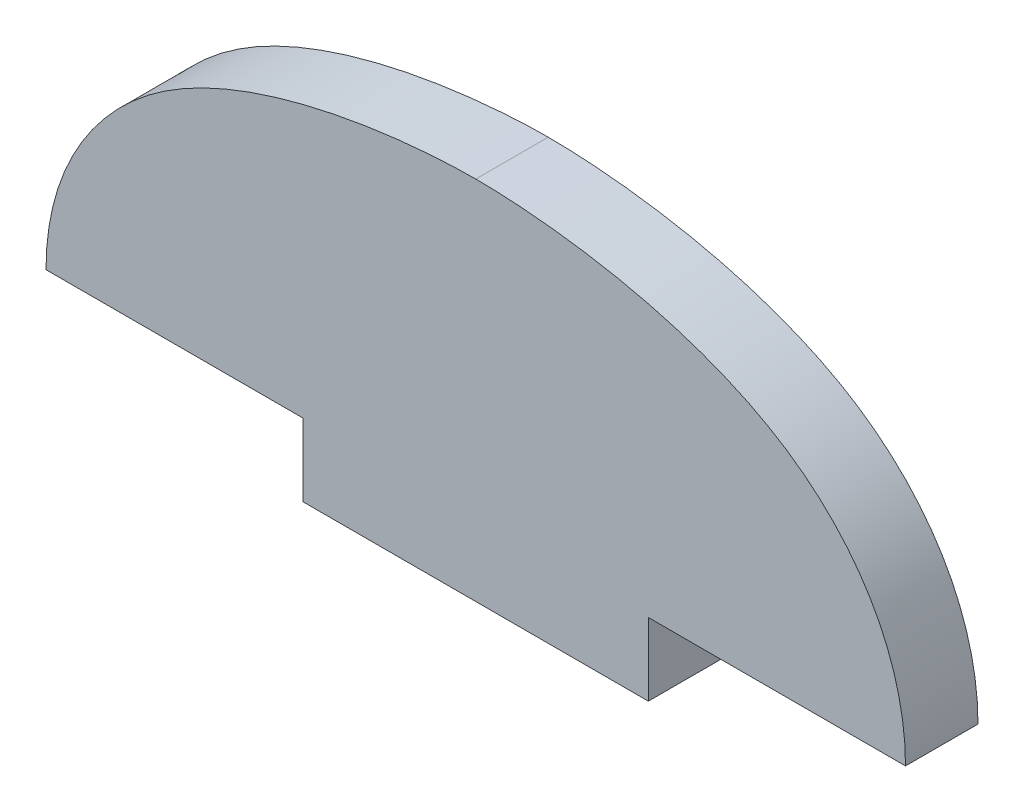
SolidWorks part; units mm, degrees
ref_plane "Front" through (0, 0, 0) normal (0, 0, 1) x (1, 0, 0)
ref_plane "Top" through (0, 0, 0) normal (0, 1, 0) x (1, 0, 0)
ref_plane "Right" through (0, 0, 0) normal (1, 0, 0) x (0, 0, -1)
sketch "Sketch1" plane through (0, 0, 0) normal (0, 0, 1) x (1, 0, 0)
  line L0 (-31.623, 41.4528) -> (31.623, 41.4528)
  line L1 (0, 41.4528) -> (0, 63.0428) construction
  line L4 (12.7, 36.1188) -> (12.7, 41.4528)
  line L5 (12.7, 41.4528) -> (-12.7, 41.4528)
  line L6 (-12.7, 41.4528) -> (-12.7, 36.1188)
  line L7 (-12.7, 36.1188) -> (12.7, 36.1188)
  line L8 (12.7, 36.1188) -> (12.7, 41.4528)
  line L9 (12.7, 41.4528) -> (-12.7, 41.4528)
  line L10 (-12.7, 41.4528) -> (-12.7, 36.1188)
  line L11 (-12.7, 36.1188) -> (12.7, 36.1188)
  spline S0 degree 3 poles (-31.623, 41.4528) (-31.623, 47.9414) (-23.8908, 61.0438) (-5.2552, 63.0428) (0, 63.0428) knots 0 0 0 0 0.432269 1 1 1 1
  spline S1 degree 3 poles (31.623, 41.4528) (31.623, 47.9414) (23.8908, 61.0438) (5.2552, 63.0428) (0, 63.0428) knots 0 0 0 0 0.432269 1 1 1 1
  point P9 (-22.9008, 57.1942)
  dimension "D2" = 21.59
  dimension "D1" = 0
extrude "Boss-Extrude1" add sketch "Sketch1" along normal blind 5.334 contours L0 L1 S0 | L1 L9 L0 S1
